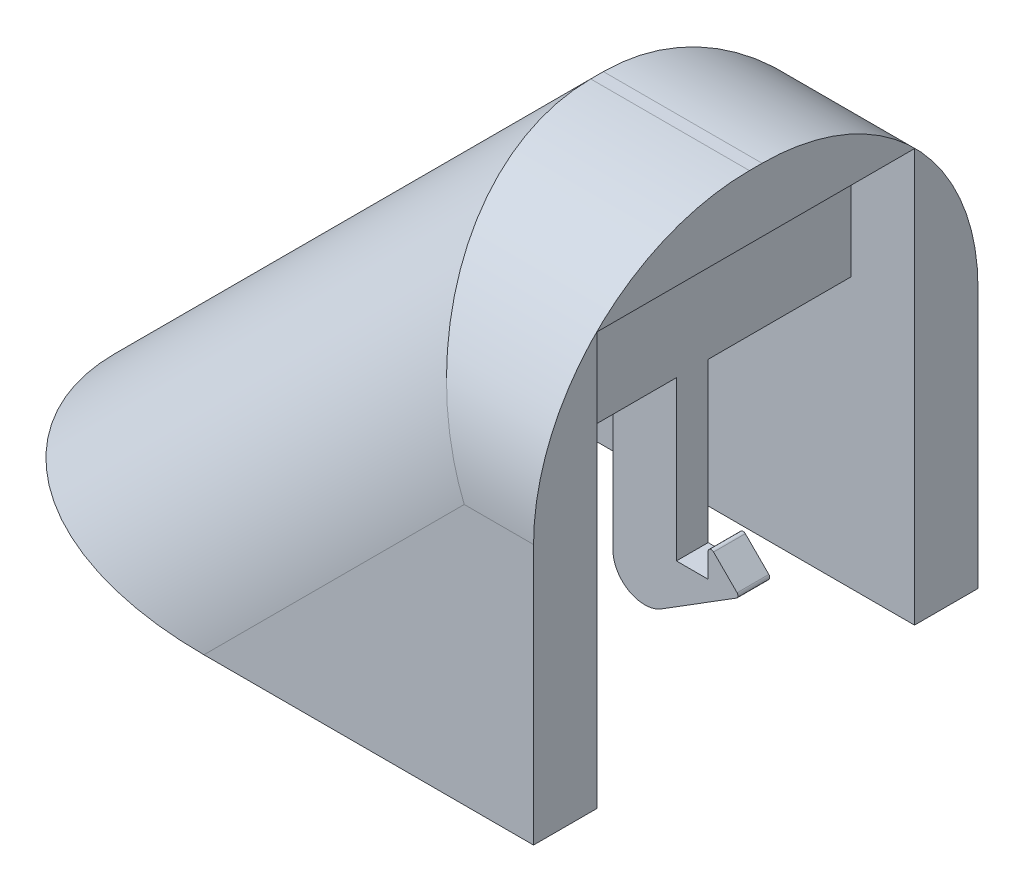
SolidWorks part; units mm, degrees
ref_plane "Front Plane" through (0, 0, 0) normal (0, 0, 1) x (1, 0, 0)
ref_plane "Top Plane" through (0, 0, 0) normal (0, 1, 0) x (1, 0, 0)
ref_plane "Right Plane" through (0, 0, 0) normal (1, 0, 0) x (0, 0, -1)
sketch "Sketch1" plane through (0, 0, 0) normal (0, 0, 1) x (1, 0, 0)
  line L0 (0, 0) -> (0, 15)
  line L1 (0, 15) -> (-5, 15)
  line L2 (-5, 15) -> (-20, 0)
  line L3 (-20, 0) -> (0, 0)
  dimension "D1" = 20
  dimension "D2" = 15
  dimension "D3" = 5
extrude "Boss-Extrude1" add sketch "Sketch1" along normal mid plane 14
shell "Shell1" thickness 2
sketch "Sketch2" plane through (0, 0, -5) normal (0, 0, 1) x (1, 0, 0)
  line L0 (0, 2) -> (0, 13) construction
  line L1 (-2, 18.5015) -> (-4, 18.5015)
  line L2 (-2, 18.5015) -> (-2, 8.5015)
  line L3 (-2, 8.5015) -> (-4, 8.5015)
  line L4 (-4, 18.5015) -> (-4, 8.5015)
  dimension "D1" = 10
  dimension "D2" = 2
  dimension "D3" = 2
extrude "Boss-Extrude2" add sketch "Sketch2" along normal up to next
sketch "Sketch3" plane through (0, 8.5015, 0) normal (0, -1, 0) x (1, 0, 0)
  line L0 (-2, 5) -> (-2, -5) construction
  line L1 (-2, 0.5) -> (-4, 0.5)
  line L2 (-2, 0.5) -> (-2, -0.5)
  line L3 (-2, -0.5) -> (-4, -0.5)
  line L4 (-4, 0.5) -> (-4, -0.5)
  line L5 (-4, 5) -> (-4, -5) construction
  line L6 (-4, -5) -> (-2, -5) construction
  dimension "D1" = 1
  dimension "D2" = 4.5
extrude "Boss-Extrude3" add sketch "Sketch3" along normal blind 5
sketch "Sketch4" plane through (0, 2, 0) normal (0, 1, 0) x (1, 0, 0)
  line L1 (0, 5) -> (-15.1716, 5)
  line L2 (0, 5) -> (0, -5)
  line L3 (0, -5) -> (-15.1716, -5)
  line L4 (-15.1716, 5) -> (-15.1716, -5)
extrude "Cut-Extrude1" cut sketch "Sketch4" against normal blind 5
sketch "Sketch5" plane through (0, 3.5015, 0) normal (0, -1, 0) x (-1, 0, 0)
  line L0 (2, -0.5) -> (4, -0.5) construction
  line L1 (4, -0.5) -> (0, -0.5)
  line L2 (4, -0.5) -> (4, 0.5)
  line L3 (4, 0.5) -> (0, 0.5)
  line L4 (0, -0.5) -> (0, 0.5)
  line L5 (2, -0.5) -> (4, -0.5) construction
  line L6 (4, -0.5) -> (4, 0.5) construction
  dimension "D1" = 1
  dimension "D2" = 4
extrude "Boss-Extrude4" add sketch "Sketch5" along normal blind 2.5
sketch "Sketch6" plane through (0, 0, 0.5) normal (0, 0, 1) x (1, 0, 0)
  line L0 (0, 3.5015) -> (-4, 1.0015)
  line L1 (-4, 1.0015) -> (0, 1.0015)
  line L2 (0, 1.0015) -> (0, 3.5015)
extrude "Cut-Extrude2" cut sketch "Sketch6" against normal up to next
sketch "Sketch7" plane through (0, 0, 0.5) normal (0, 0, 1) x (1, 0, 0)
  line L0 (0, 3.5015) -> (-1, 3.5015)
  line L1 (0, 3.5015) -> (-2, 3.5015) construction
  line L4 (-1, 3.5015) -> (-1, 4.5015)
  line L5 (-1, 4.5015) -> (0, 3.5015)
  dimension "D1" = 1
extrude "Boss-Extrude5" add sketch "Sketch7" against normal up to vertex
fillet "Fillet2" radius 0.1 2 edges at (-1, 4.5015, 0) (0, 3.5015, 0)
fillet "Fillet3" radius 1 1 edges at (-4, 1.0015, 0)
fillet "Fillet4" radius 6.8 4 edges at (-12.5, 7.5, -7) (-2.5, 15, -7) (-12.5, 7.5, 7) (-2.5, 15, 7)
